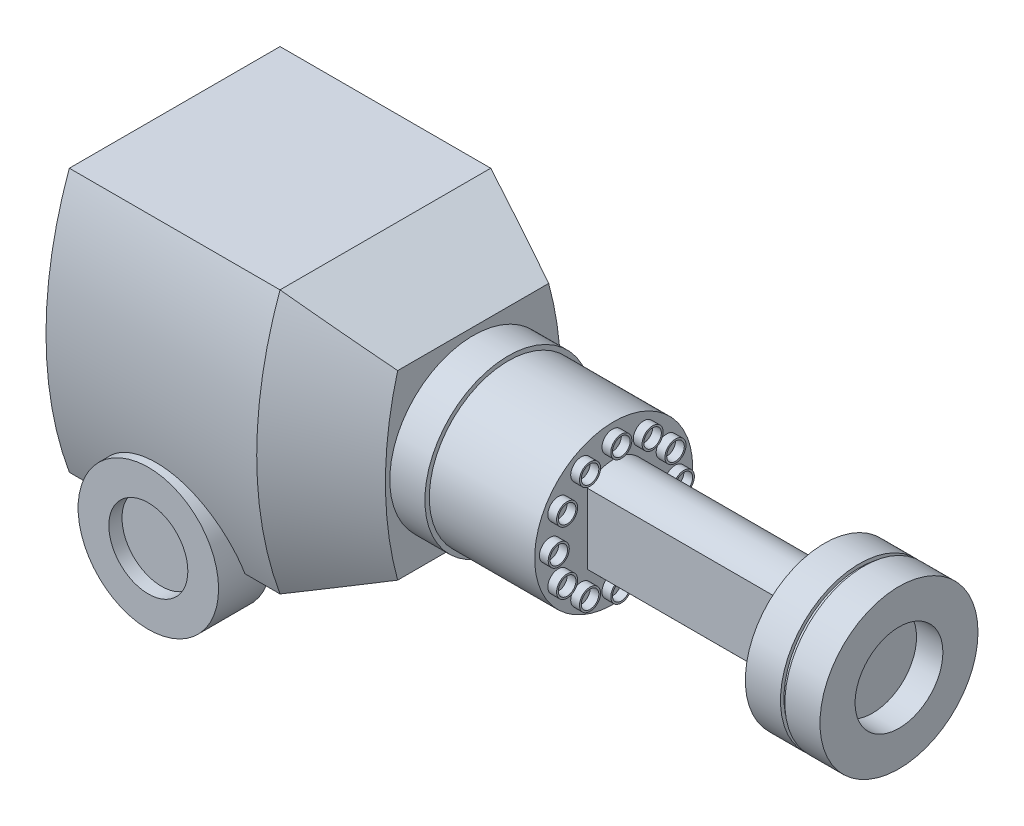
SolidWorks part; units mm, degrees
ref_plane "Front Plane" through (0, 0, 0) normal (0, 0, 1) x (1, 0, 0)
ref_plane "Top Plane" through (0, 0, 0) normal (0, 1, 0) x (1, 0, 0)
ref_plane "Right Plane" through (0, 0, 0) normal (1, 0, 0) x (0, 0, -1)
sketch "Sketch2" plane through (0, 0, 0) normal (1, 0, 0) x (0, 0, -1)
  line L0 (41.5977, 0) -> (-48.0934, 0) construction
  line L1 (0, 33.4156) -> (0, -39.1618) construction
  line L2 (-15.24, 19.05) -> (15.24, 19.05)
  line L3 (-15.24, -19.05) -> (15.24, -19.05)
  arc A0 (15.24, 19.05) -> (15.24, -19.05) centre (-36.867, 0) cw
  arc A1 (-15.24, 19.05) -> (-15.24, -19.05) centre (36.867, 0) ccw
  point P11 (0, -19.05)
  point P13 (0, 19.05)
  dimension "D1" = 15.24
  dimension "D2" = 19.05
  dimension "D3" = 19.05
  dimension "D4" = 15.24
extrude "Boss-Extrude1" add sketch "Sketch2" along normal blind 30.48
sketch "Sketch7" plane through (30.48, 0, 0) normal (1, 0, 0) x (0, 0, -1)
sketch "Sketch8" plane through (30.48, 0, 0) normal (1, 0, 0) x (0, 0, -1)
  line L4 (15.24, 19.05) -> (-15.24, 19.05)
  line L5 (-15.24, -19.05) -> (15.24, -19.05)
  line L6 (15.24, 19.05) -> (-15.24, 19.05)
  line L7 (-15.24, -19.05) -> (15.24, -19.05)
  arc A4 (15.24, -19.05) -> (15.24, 19.05) centre (-36.867, 0) ccw
  arc A5 (-15.24, 19.05) -> (-15.24, -19.05) centre (36.867, 0) ccw
  arc A6 (15.24, -19.05) -> (15.24, 19.05) centre (-36.867, 0) ccw
  arc A7 (-15.24, 19.05) -> (-15.24, -19.05) centre (36.867, 0) ccw
  dimension "D1" = 0
extrude "Boss-Extrude2" add sketch "Sketch8" along normal blind 12.7 draft 25
sketch "Sketch9" plane through (43.18, 0, 0) normal (1, 0, 0) x (0, 0, -1)
  circle A0 centre (0, 0) radius 12.065
  dimension "D1" = 24.13
extrude "Boss-Extrude3" add sketch "Sketch9" along normal blind 5.08
sketch "Sketch10" plane through (48.26, 0, 0) normal (1, 0, 0) x (0, 0, -1)
  circle A1 centre (0, 0) radius 11.43
  dimension "D1" = 22.86
extrude "Boss-Extrude4" add sketch "Sketch10" along normal blind 15.24
sketch "Sketch12" plane through (63.5, 0, 0) normal (1, 0, 0) x (0, 0, -1)
  circle A0 centre (8.89, 0) radius 1.524
  circle A1 centre (8.89, 0) radius 1.27
  dimension "D1" = 3.048
  dimension "D2" = 2.54
  dimension "D3" = 8.89
extrude "Boss-Extrude6" add sketch "Sketch12" along normal blind 1.27
pattern_circular "CirPattern2" count 12 over 360 about axis through (0, 0, 0.1609) along (1, 0, 0) of "Boss-Extrude6"
sketch "Sketch13" plane through (63.5, 0, 0) normal (1, 0, 0) x (0, 0, -1)
  line L0 (-4.4542, 0) -> (5.3557, 0) construction
  line L1 (0, -5.7004) -> (0, 6.2306) construction
  line L2 (3.81, 5.0005) -> (3.81, -5.1595)
  line L3 (-3.81, 5.0005) -> (-3.81, -5.1595)
  arc A0 (-3.81, 5.0005) -> (3.81, 5.0005) centre (0, 1.6404) cw
  arc A1 (-3.81, -5.1595) -> (3.81, -5.1595) centre (0, -1.7994) ccw
  point P7 (3.81, -0.0795)
  dimension "D3" = 5.08
  dimension "D4" = 5.08
  dimension "D1" = 3.81
  dimension "D2" = 5.08
extrude "Boss-Extrude7" add sketch "Sketch13" along normal blind 30.48
sketch "Sketch14" plane through (93.98, 0, 0) normal (1, 0, 0) x (0, 0, -1)
  circle A0 centre (0, 0) radius 11.43
extrude "Boss-Extrude8" add sketch "Sketch14" along normal blind 5.08
sketch "Sketch15" plane through (99.06, 0, 0) normal (1, 0, 0) x (0, 0, -1)
  circle A0 centre (0, 0) radius 10.922
  circle A1 centre (0, 0) radius 11.43 construction
  dimension "D1" = 0.508
extrude "Boss-Extrude9" add sketch "Sketch15" along normal blind 0.635
sketch "Sketch16" plane through (99.695, 0, 0) normal (1, 0, 0) x (0, 0, -1)
  circle A0 centre (0, 0) radius 11.43
extrude "Boss-Extrude10" add sketch "Sketch16" along normal blind 5.08
ref_plane "Plane1" through (0, 0, 15.24) normal (0, 0, 1) x (1, 0, 0)
sketch "Sketch17" plane through (0, 0, 15.24) normal (0, 0, 1) x (1, 0, 0)
  line L0 (30.48, -19.05) -> (0, -19.05) construction
  circle A0 centre (15.24, -19.05) radius 10.16
  dimension "D1" = 20.32
extrude "Boss-Extrude14" add sketch "Sketch17" along normal mid plane 7.62
sketch "Sketch19" plane through (0, 0, 11.43) normal (0, 0, -1) x (-1, 0, 0)
  line L0 (-19.4185, -19.05) -> (-10.5272, -19.05)
  line L1 (-30.48, -19.05) -> (0, -19.05) construction
  line L2 (-5.08, -19.05) -> (-25.4, -19.05) construction
  line L3 (-10.5272, -19.05) -> (-10.5272, -26.67)
  line L4 (-19.4185, -19.05) -> (-19.4185, -26.67)
  arc A0 (-19.4185, -26.67) -> (-10.5272, -26.67) centre (-14.9729, -22.2244) ccw
  point P7 (-14.9729, -19.05)
  dimension "D1" = 8.8913
  dimension "D2" = 7.62
  dimension "D3" = 7.62
extrude "Boss-Extrude15" add sketch "Sketch19" along normal blind 12.7
sketch "Sketch20" plane through (19.4185, 0, 0) normal (1, 0, 0) x (0, 0, -1)
  line L0 (1.27, -19.05) -> (12.9263, -19.05)
  line L1 (-15.24, -19.05) -> (15.24, -19.05) construction
  line L2 (1.27, -19.05) -> (1.27, -29.0438)
  arc A0 (12.9263, -19.05) -> (1.27, -29.0438) centre (-2.4156, -12.9504) cw
  dimension "D1" = 16.51
extrude "Boss-Extrude16" add sketch "Sketch20" against normal blind 8.89
sketch "Sketch21" plane through (0, 0, -1.27) normal (0, 0, 1) x (1, 0, 0)
  line L6 (10.5285, -26.6713) -> (10.5285, -29.0438)
  line L7 (10.5285, -29.0438) -> (19.4185, -29.0438)
  line L8 (19.4185, -29.0438) -> (19.4185, -26.67)
  line L9 (10.5285, -26.6713) -> (10.5285, -29.0438)
  line L10 (10.5285, -29.0438) -> (19.4185, -29.0438)
  line L11 (19.4185, -29.0438) -> (19.4185, -26.67)
  arc A2 (10.5285, -26.6713) -> (19.4185, -26.67) centre (14.9729, -22.2244) ccw
  arc A3 (10.5285, -26.6713) -> (19.4185, -26.67) centre (14.9729, -22.2244) ccw
  dimension "D1" = 0
extrude "Cut-Extrude1" cut sketch "Sketch21" against normal blind 8.89
sketch "Sketch22" plane through (104.775, 0, 0) normal (1, 0, 0) x (0, 0, -1)
  circle A0 centre (0, 0) radius 6.35
  dimension "D1" = 12.7
extrude "Cut-Extrude2" cut sketch "Sketch22" against normal blind 3.81
sketch "Sketch23" plane through (0, 0, 19.05) normal (0, 0, 1) x (1, 0, 0)
  circle A0 centre (15.24, -19.05) radius 5.715
  dimension "D1" = 11.43
extrude "Cut-Extrude4" cut sketch "Sketch23" against normal blind 1.905
